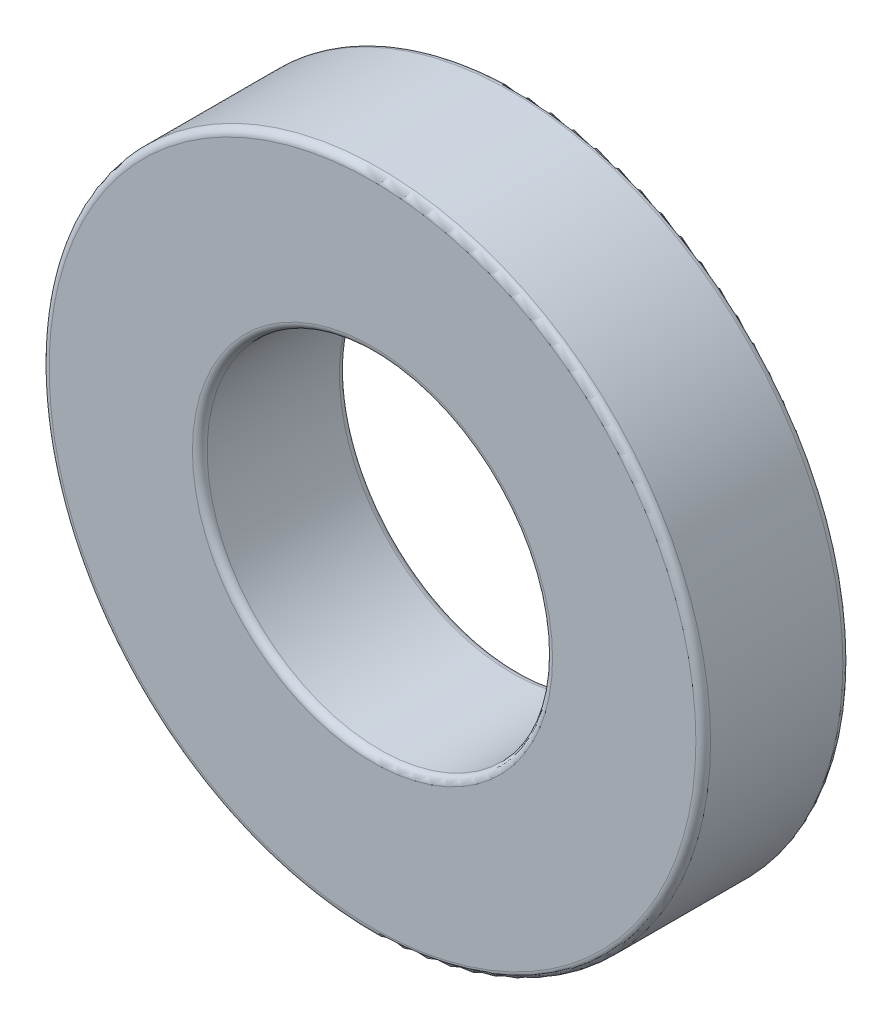
SolidWorks part; units mm, degrees
ref_plane "Front" through (0, 0, 0) normal (0, 0, 1) x (1, 0, 0)
ref_plane "Top" through (0, 0, 0) normal (0, 1, 0) x (1, 0, 0)
ref_plane "Right" through (0, 0, 0) normal (1, 0, 0) x (0, 0, -1)
sketch "草图1" plane through (0, 0, 0) normal (0, 0, 1) x (1, 0, 0)
  circle A0 centre (0, 0) radius 4.5
  circle A1 centre (0, 0) radius 2.35
  dimension "D1" = 9
  dimension "D2" = 4.7
extrude "凸台-拉伸1" add sketch "草图1" along normal blind 2
fillet "圆角1" radius 0.1 4 edges at (4.5, 0, 0) (4.5, 0, 2) (2.35, 0, 0) (2.35, 0, 2)
